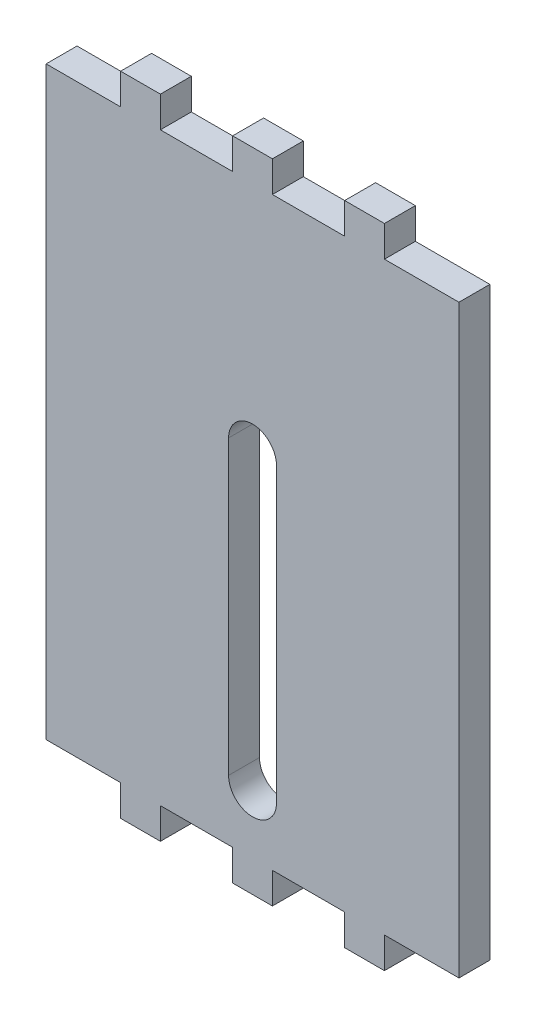
SolidWorks part; units mm, degrees
ref_plane "Front Plane" through (0, 0, 0) normal (0, 0, 1) x (1, 0, 0)
ref_plane "Top Plane" through (0, 0, 0) normal (0, 1, 0) x (1, 0, 0)
ref_plane "Right Plane" through (0, 0, 0) normal (1, 0, 0) x (0, 0, -1)
sketch "Sketch1" plane through (0, 0, 0) normal (0, 0, 1) x (1, 0, 0)
  line L0 (-21.15, 21.15) -> (21.15, 21.15) construction
  line L1 (-21.15, 38.85) -> (21.15, 38.85)
  line L2 (-21.15, 38.85) -> (-21.15, -21.15)
  line L3 (-21.15, -21.15) -> (21.15, -21.15)
  line L4 (21.15, 38.85) -> (21.15, -21.15)
  line L5 (2, -24.325) -> (2, -21.15)
  line L6 (-13.5, -21.15) -> (-9.5, -21.15)
  line L7 (-13.5, -21.15) -> (-13.5, -24.325)
  line L8 (-13.5, -24.325) -> (-9.5, -24.325)
  line L9 (-9.5, -21.15) -> (-9.5, -24.325)
  line L10 (2, -24.325) -> (-2, -24.325)
  line L11 (2, -21.15) -> (-2, -21.15)
  line L12 (-2, -24.325) -> (-2, -21.15)
  line L13 (2, -24.325) -> (-2, -21.15) construction
  line L14 (2, -21.15) -> (-2, -24.325) construction
  line L15 (-21.15, 8.85) -> (21.15, 8.85) construction
  line L16 (13.5, -21.15) -> (9.5, -21.15)
  line L17 (13.5, -21.15) -> (13.5, -24.325)
  line L18 (13.5, -24.325) -> (9.5, -24.325)
  line L19 (9.5, -21.15) -> (9.5, -24.325)
  line L20 (2, 38.85) -> (-2, 42.025) construction
  line L21 (2, 42.025) -> (-2, 38.85) construction
  line L22 (9.5, 38.85) -> (9.5, 42.025)
  line L23 (13.5, 42.025) -> (9.5, 42.025)
  line L24 (13.5, 38.85) -> (13.5, 42.025)
  line L25 (-2, 42.025) -> (-2, 38.85)
  line L26 (2, 42.025) -> (-2, 42.025)
  line L27 (-9.5, 38.85) -> (-9.5, 42.025)
  line L28 (-13.5, 42.025) -> (-9.5, 42.025)
  line L29 (-13.5, 38.85) -> (-13.5, 42.025)
  line L30 (2, 42.025) -> (2, 38.85)
  line L31 (-13.5, 40.4375) -> (13.5, 40.4375)
  line L33 (-2.5, 15) -> (2.5, 15)
  line L34 (-2.5, 15) -> (-2.5, -15)
  line L35 (-2.5, -15) -> (2.5, -15)
  line L36 (2.5, 15) -> (2.5, -15)
  arc A1 (-2.5, 15) -> (2.5, 15) centre (0, 15) cw
  arc A2 (2.5, -15) -> (-2.5, -15) centre (0, -15) cw
  point P13 (0, -21.15)
  point P14 (0, -22.7375)
  point P37 (0, 40.4375)
  point P41 (0, 40.4375)
  dimension "D1" = 42.3
  dimension "D3" = 42.3
  dimension "D4" = 21.15
  dimension "D5" = 21.15
  dimension "D2" = 60
  dimension "D8" = 4
  dimension "D9" = 3.175
  dimension "D6" = 5
  dimension "D11" = 2.5
  dimension "D12" = 30
  dimension "D13" = 15
  dimension "D7" = 7.5
  dimension "D10" = 7.5
extrude "Boss-Extrude1" add sketch "Sketch1" along normal blind 3.175 contours L4 L1 L2 L3 L36 A2 L34 A1 | L29 L31 L27 L28 | L31 L29 L1 L27 | L25 L31 L30 L26 | L31 L25 L1 L30 | L22 L31 L24 L23 | L31 L22 L1 L24 | L9 L3 L7 L8 | L3 L19 L18 L17 | L12 L10 L5 L3
sketch "Sketch2" plane through (0, 0, 3.175) normal (0, 0, 1) x (1, 0, 0)
  line L37 (-2.4594, 15) -> (-2.4594, -15)
  line L38 (2.4594, -15) -> (2.4594, 15)
  line L39 (-2.4594, 15) -> (-2.4594, -15)
  line L40 (2.4594, -15) -> (2.4594, 15)
  line L56 (21.1906, -21.1906) -> (21.1906, 38.8906)
  line L57 (21.1906, 38.8906) -> (13.5406, 38.8906)
  line L58 (13.5406, 38.8906) -> (13.5406, 42.0656)
  line L59 (13.5406, 42.0656) -> (9.4594, 42.0656)
  line L60 (9.4594, 42.0656) -> (9.4594, 38.8906)
  line L61 (9.4594, 38.8906) -> (2.0406, 38.8906)
  line L62 (2.0406, 38.8906) -> (2.0406, 42.0656)
  line L63 (2.0406, 42.0656) -> (-2.0406, 42.0656)
  line L64 (-2.0406, 42.0656) -> (-2.0406, 38.8906)
  line L65 (-2.0406, 38.8906) -> (-9.4594, 38.8906)
  line L66 (-9.4594, 38.8906) -> (-9.4594, 42.0656)
  line L67 (-9.4594, 42.0656) -> (-13.5406, 42.0656)
  line L68 (-13.5406, 42.0656) -> (-13.5406, 38.8906)
  line L69 (-13.5406, 38.8906) -> (-21.1906, 38.8906)
  line L70 (-21.1906, 38.8906) -> (-21.1906, -21.1906)
  line L71 (-21.1906, -21.1906) -> (-13.5406, -21.1906)
  line L72 (-13.5406, -21.1906) -> (-13.5406, -24.3656)
  line L73 (-13.5406, -24.3656) -> (-9.4594, -24.3656)
  line L74 (-9.4594, -24.3656) -> (-9.4594, -21.1906)
  line L75 (-9.4594, -21.1906) -> (-2.0406, -21.1906)
  line L76 (-2.0406, -21.1906) -> (-2.0406, -24.3656)
  line L77 (-2.0406, -24.3656) -> (2.0406, -24.3656)
  line L78 (2.0406, -24.3656) -> (2.0406, -21.1906)
  line L79 (2.0406, -21.1906) -> (9.4594, -21.1906)
  line L80 (9.4594, -21.1906) -> (9.4594, -24.3656)
  line L81 (9.4594, -24.3656) -> (13.5406, -24.3656)
  line L82 (13.5406, -24.3656) -> (13.5406, -21.1906)
  line L83 (13.5406, -21.1906) -> (21.1906, -21.1906)
  line L84 (21.1906, -21.1906) -> (21.1906, 38.8906)
  line L85 (21.1906, 38.8906) -> (13.5406, 38.8906)
  line L86 (13.5406, 38.8906) -> (13.5406, 42.0656)
  line L87 (13.5406, 42.0656) -> (9.4594, 42.0656)
  line L88 (9.4594, 42.0656) -> (9.4594, 38.8906)
  line L89 (9.4594, 38.8906) -> (2.0406, 38.8906)
  line L90 (2.0406, 38.8906) -> (2.0406, 42.0656)
  line L91 (2.0406, 42.0656) -> (-2.0406, 42.0656)
  line L92 (-2.0406, 42.0656) -> (-2.0406, 38.8906)
  line L93 (-2.0406, 38.8906) -> (-9.4594, 38.8906)
  line L94 (-9.4594, 38.8906) -> (-9.4594, 42.0656)
  line L95 (-9.4594, 42.0656) -> (-13.5406, 42.0656)
  line L96 (-13.5406, 42.0656) -> (-13.5406, 38.8906)
  line L97 (-13.5406, 38.8906) -> (-21.1906, 38.8906)
  line L98 (-21.1906, 38.8906) -> (-21.1906, -21.1906)
  line L99 (-21.1906, -21.1906) -> (-13.5406, -21.1906)
  line L100 (-13.5406, -21.1906) -> (-13.5406, -24.3656)
  line L101 (-13.5406, -24.3656) -> (-9.4594, -24.3656)
  line L102 (-9.4594, -24.3656) -> (-9.4594, -21.1906)
  line L103 (-9.4594, -21.1906) -> (-2.0406, -21.1906)
  line L104 (-2.0406, -21.1906) -> (-2.0406, -24.3656)
  line L105 (-2.0406, -24.3656) -> (2.0406, -24.3656)
  line L106 (2.0406, -24.3656) -> (2.0406, -21.1906)
  line L107 (2.0406, -21.1906) -> (9.4594, -21.1906)
  line L108 (9.4594, -21.1906) -> (9.4594, -24.3656)
  line L109 (9.4594, -24.3656) -> (13.5406, -24.3656)
  line L110 (13.5406, -24.3656) -> (13.5406, -21.1906)
  line L111 (13.5406, -21.1906) -> (21.1906, -21.1906)
  arc A5 (-2.4594, -15) -> (2.4594, -15) centre (0, -15) ccw
  arc A6 (2.4594, 15) -> (-2.4594, 15) centre (0, 15) ccw
  arc A7 (-2.4594, -15) -> (2.4594, -15) centre (0, -15) ccw
  arc A8 (2.4594, 15) -> (-2.4594, 15) centre (0, 15) ccw
  dimension "D1" = 0.0406
  dimension "D2" = 0.0406
extrude "Boss-Extrude2" add sketch "Sketch2" against normal blind 3.175
equation "\"stepper width\"=4.23"
equation "\"stepper hole disctance\" = 3.1"
equation "\"stepper hole diameter\"=0.34"
equation "\"stepper shaft hole\"=2.4"
equation "\"tooth width\"=0.4"
equation "\"tooth thickness\"=0.3175"
equation "\"tooth to side\"=0.75"
equation "\"motor chamber height\"= 6"
equation "\"D1@Sketch1\"=\"stepper width\""
equation "\"D3@Sketch1\"=\"stepper width\""
equation "\"D4@Sketch1\"=\"stepper width\"/2"
equation "\"D5@Sketch1\"=\"stepper width\"/2"
equation "\"gear shaft diameter\"= 0.5"
equation "\"D2@Sketch1\"=\"motor chamber height\""
equation "\"D8@Sketch1\"=\"tooth width\""
equation "\"D9@Sketch1\"=\"tooth thickness\""
equation "\"D1@Boss-Extrude1\"=\"tooth thickness\""
equation "\"D6@Sketch1\"=\"gear shaft diameter\""
equation "\"D11@Sketch1\"=\"gear shaft diameter\"/2"
equation "\"D12@Sketch1\"=\"motor chamber height\"/2"
equation "\"D13@Sketch1\"=\"motor chamber height\"/4"
equation "\"D7@Sketch1\"=\"tooth to side\""
equation "\"D10@Sketch1\"=\"tooth to side\""
equation "\"D5@Sketch1\"=\"stepper hole diameter\""
